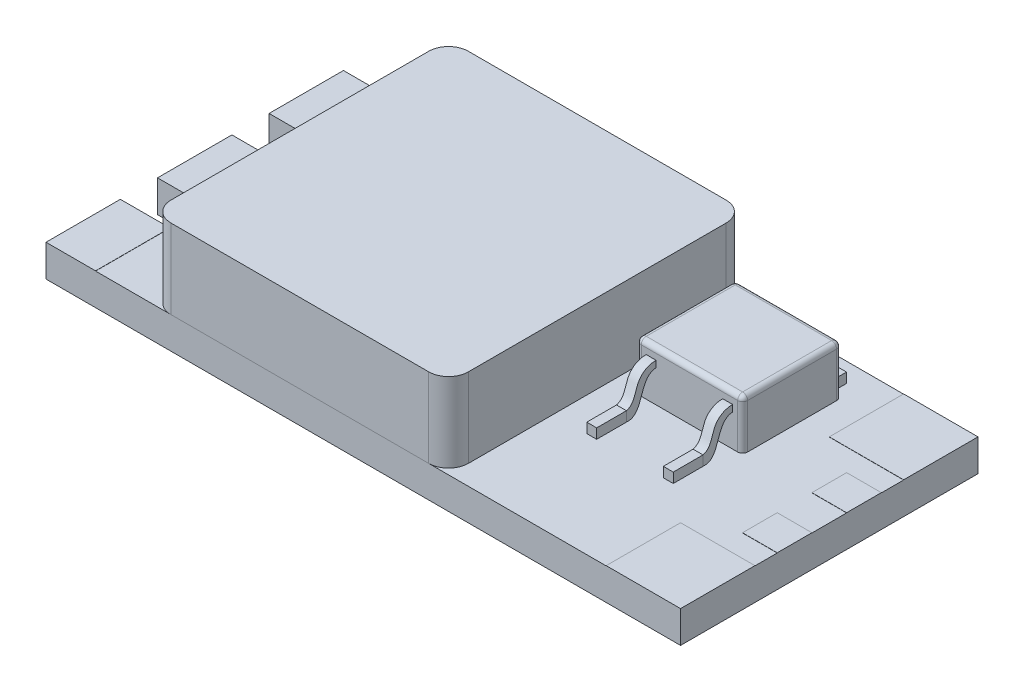
SolidWorks part; units mm, degrees
ref_plane "Front Plane" through (0, 0, 0) normal (0, 0, 1) x (1, 0, 0)
ref_plane "Top Plane" through (0, 0, 0) normal (0, 1, 0) x (1, 0, 0)
ref_plane "Right Plane" through (0, 0, 0) normal (1, 0, 0) x (0, 0, -1)
sketch "Sketch1" plane through (0, 0, 0) normal (0, 1, 0) x (1, 0, 0)
  line L0 (0, 3.75) -> (2.5, 3.75)
  line L1 (0, 0) -> (32, 0)
  line L2 (0, 0) -> (0, 3.75)
  line L3 (0, 15) -> (32, 15)
  line L4 (32, 0) -> (32, 15)
  line L5 (0, 0) -> (2.5, 0)
  line L6 (0, 0) -> (0, 3.75)
  line L7 (0, 15) -> (2.5, 15)
  line L8 (2.5, 3.75) -> (2.5, 5.625)
  line L9 (0, 11.25) -> (2.5, 11.25)
  line L10 (0, 11.25) -> (0, 15)
  line L11 (0, 9.375) -> (2.5, 9.375)
  line L12 (0, 9.375) -> (0, 5.625)
  line L13 (0, 5.625) -> (2.5, 5.625)
  line L15 (0, 11.25) -> (0, 15)
  line L16 (0, 5.625) -> (0, 9.375)
  line L17 (0, 5.625) -> (0, 9.375)
  line L18 (2.5, 9.375) -> (2.5, 11.25)
  dimension "D1" = 15
  dimension "D2" = 32
  dimension "D3" = 2.5
  dimension "D4" = 3.75
  dimension "D5" = 3.75
  dimension "D6" = 3.75
  dimension "D7" = 1.875
extrude "Boss-Extrude1" add sketch "Sketch1" along normal blind 1.6 contours L18 L11 L12 L13 L8 L0 L2 L1 L4 L3 L10 L9
sketch "Sketch2" plane through (0, 1.6, 0) normal (0, 1, 0) x (1, 0, 0)
  line L0 (0, 0) -> (32, 0) construction
  line L1 (5.3, 0) -> (20.3, 0)
  line L2 (5.3, 0) -> (5.3, 15)
  line L3 (5.3, 15) -> (20.3, 15)
  line L4 (20.3, 0) -> (20.3, 15)
  line L5 (0, 15) -> (32, 15) construction
  line L6 (0, 9.375) -> (0, 5.625) construction
  dimension "D1" = 5.3
  dimension "D2" = 15
extrude "Boss-Extrude2" add sketch "Sketch2" along normal blind 4 separate body
fillet "Fillet1" radius 1 4 edges at (20.3, 3.6, 0) (20.3, 3.6, -15) (5.3, 3.6, -15) (5.3, 3.6, 0)
sketch "Sketch3" plane through (0, 1.6, 0) normal (0, 1, 0) x (1, 0, 0)
  line L0 (32, 7.5) -> (33.6122, 7.5)
  line L1 (0, 15) -> (2.5, 15)
  line L2 (0, 15) -> (0, 3.75)
  line L3 (0, 3.75) -> (2.5, 3.75)
  line L4 (2.5, 15) -> (2.5, 3.75)
  line L5 (0, 0) -> (2.5, 0)
  line L6 (0, 0) -> (0, 3.75)
  line L7 (0, 3.75) -> (2.5, 3.75)
  line L8 (2.5, 0) -> (2.5, 3.75)
  line L9 (32, 0) -> (28.25, 0)
  line L10 (32, 0) -> (32, 3.75)
  line L11 (32, 3.75) -> (28.25, 3.75)
  line L12 (2.5, 11.25) -> (2.5, 9.375)
  line L13 (2.5, 9.375) -> (0, 9.375)
  line L14 (0, 9.375) -> (0, 5.625)
  line L15 (0, 5.625) -> (2.5, 5.625)
  line L16 (2.5, 5.625) -> (2.5, 3.75)
  line L17 (2.5, 3.75) -> (0, 3.75)
  line L18 (0, 3.75) -> (0, 0)
  line L19 (0, 0) -> (32, 0)
  line L20 (32, 0) -> (32, 15)
  line L21 (32, 15) -> (0, 15)
  line L22 (0, 15) -> (0, 11.25)
  line L23 (0, 11.25) -> (2.5, 11.25)
  line L24 (2.5, 11.25) -> (2.5, 9.375)
  line L25 (2.5, 9.375) -> (0, 9.375)
  line L26 (0, 9.375) -> (0, 5.625)
  line L27 (0, 5.625) -> (2.5, 5.625)
  line L28 (2.5, 5.625) -> (2.5, 3.75)
  line L29 (2.5, 3.75) -> (0, 3.75)
  line L30 (0, 3.75) -> (0, 0)
  line L31 (0, 0) -> (32, 0)
  line L32 (32, 0) -> (32, 15)
  line L33 (32, 15) -> (0, 15)
  line L34 (0, 15) -> (0, 11.25)
  line L35 (0, 11.25) -> (2.5, 11.25)
  line L36 (28.25, 0) -> (28.25, 3.75)
  line L37 (32, 6.625) -> (30.25, 6.625)
  line L38 (32, 6.625) -> (32, 4.875)
  line L39 (32, 4.875) -> (30.25, 4.875)
  line L40 (30.25, 6.625) -> (30.25, 4.875)
  line L41 (30.25, 8.375) -> (30.25, 10.125)
  line L42 (32, 10.125) -> (30.25, 10.125)
  line L43 (32, 8.375) -> (32, 10.125)
  line L44 (32, 8.375) -> (30.25, 8.375)
  line L45 (28.25, 15) -> (28.25, 11.25)
  line L46 (32, 11.25) -> (28.25, 11.25)
  line L47 (32, 15) -> (32, 11.25)
  line L48 (32, 15) -> (28.25, 15)
  line M27 (2.5, 9.375) -> (0, 9.375)
  line M28 (0, 9.375) -> (0, 5.625)
  line M29 (0, 5.625) -> (2.5, 5.625)
  line M31 (2.5, 3.75) -> (0, 3.75)
  line M32 (0, 3.75) -> (0, 0)
  line M33 (0, 0) -> (32, 0)
  line M34 (32, 0) -> (32, 15)
  line M35 (32, 15) -> (0, 15)
  line M36 (0, 15) -> (0, 11.25)
  line M37 (0, 11.25) -> (2.5, 11.25)
  dimension "D2" = 3.75
  dimension "D3" = 3.75
  dimension "D4" = 1.75
  dimension "D5" = 1.75
  dimension "D6" = 0.875
  dimension "D1" = 0
extrude "Boss-Extrude3" add sketch "Sketch3" along normal blind 0.01 contours L46 L45 M34 M35 | L44 L32 L42 L41 | L37 L40 L39 L32 | L36 L11 M33 M34 | L4 M35 M36 M37 | L4 M27 M28 M29 | L8 M33 M31 M32
sketch "Sketch4" plane through (0, 1.6, 0) normal (0, 1, 0) x (1, 0, 0)
  line L1 (21.4824, 13.2754) -> (26.844, 13.2754)
  line L2 (21.4824, 13.2754) -> (21.4824, 8.2878)
  line L3 (21.4824, 8.2878) -> (26.844, 8.2878)
  line L4 (26.844, 13.2754) -> (26.844, 8.2878)
extrude "Boss-Extrude4" add sketch "Sketch4" along normal blind 2.5 contours L2 L1 L4 L3
sketch "Sketch6" plane through (0, 1.6, 0) normal (0, 1, 0) x (1, 0, 0)
  line L1 (21.9824, 13.2754) -> (26.344, 13.2754)
  line L2 (21.9824, 13.2754) -> (21.9824, 14.0254)
  line L3 (21.9824, 14.0254) -> (26.344, 14.0254)
  line L4 (21.4824, 8.2878) -> (26.844, 8.2878)
  line L5 (26.844, 8.2878) -> (26.844, 13.2754)
  line L6 (26.844, 13.2754) -> (21.4824, 13.2754)
  line L7 (21.4824, 13.2754) -> (21.4824, 8.2878)
  line L8 (21.4824, 8.2878) -> (26.844, 8.2878)
  line L9 (26.844, 8.2878) -> (26.844, 13.2754)
  line L10 (26.844, 13.2754) -> (21.4824, 13.2754)
  line L11 (21.4824, 13.2754) -> (21.4824, 8.2878)
  line L12 (26.344, 13.2754) -> (26.344, 14.0254)
  line L14 (21.9824, 8.2878) -> (22.4824, 8.2878)
  line L15 (21.9824, 8.2878) -> (21.9824, 5.2878)
  line L16 (21.9824, 5.2878) -> (22.4824, 5.2878)
  line L17 (22.4824, 8.2878) -> (22.4824, 5.2878)
  line L18 (26.344, 8.2878) -> (25.844, 8.2878)
  line L19 (26.344, 8.2878) -> (26.344, 5.2878)
  line L20 (26.344, 5.2878) -> (25.844, 5.2878)
  line L21 (25.844, 8.2878) -> (25.844, 5.2878)
  line L22 (25.844, 5.2878) -> (26.344, 5.2878)
  line L23 (25.844, 5.2878) -> (25.844, 6.6282)
  line L25 (26.344, 5.2878) -> (26.344, 6.6282)
  line L26 (21.9824, 5.2878) -> (22.4824, 5.2878)
  line L27 (21.9824, 5.2878) -> (21.9824, 6.7878)
  line L28 (21.9824, 6.7878) -> (22.4824, 6.7878)
  line L29 (22.4824, 5.2878) -> (22.4824, 6.7878)
  line L30 (25.844, 5.2878) -> (26.344, 5.2878)
  line L31 (25.844, 5.2878) -> (25.844, 6.7878)
  line L32 (25.844, 6.7878) -> (26.344, 6.7878)
  line L33 (26.344, 5.2878) -> (26.344, 6.7878)
  line M38 (21.4824, 13.2754) -> (26.844, 13.2754)
  dimension "D2" = 0.75
  dimension "D3" = 0.5
  dimension "D4" = 0.5
  dimension "D5" = 0.5
  dimension "D6" = 0.5
  dimension "D7" = 0.5
  dimension "D8" = 0.5
  dimension "D9" = 3
  dimension "D10" = 3
  dimension "D1" = 0
extrude "Boss-Extrude5" add sketch "Sketch6" along normal blind 0.5 separate body contours L32 L21 L20 L19 | L28 L15 L16 L17 | L12 L3 L2 M38
sketch "Sketch7" plane through (26.344, 0, 0) normal (1, 0, 0) x (0, 0, -1)
  line L0 (8.2878, 4.1) -> (8.2878, 1.6) construction
  line L1 (8.2878, 3.2266) -> (8.2878, 3.5498)
  line L5 (5.2878, 1.6) -> (6.7878, 1.6)
  line L6 (6.7878, 1.6) -> (6.7878, 2.1)
  line L7 (6.7878, 2.1) -> (5.2878, 2.1)
  line L8 (5.2878, 2.1) -> (5.2878, 1.6)
  line L9 (5.2878, 1.6) -> (6.7878, 1.6)
  line L10 (6.7878, 1.6) -> (6.7878, 2.1)
  line L11 (6.7878, 2.1) -> (5.2878, 2.1)
  line L12 (5.2878, 2.1) -> (5.2878, 1.6)
  spline S0 degree 3 poles (6.7878, 1.6) (7.7188, 1.5101) (7.3747, 3.1846) (8.2878, 3.2266) knots 0 0 0 0 1 1 1 1
  spline S1 degree 3 poles (6.7878, 2.1) (7.2302, 2.2154) (7.1923, 3.1943) (7.9475, 3.5661) (8.2878, 3.5498) knots 0 0 0 0 0.555689 1 1 1 1
  line M6 (6.7878, 1.6) -> (6.7878, 2.1)
  dimension "D1" = 0
extrude "Boss-Extrude6" add sketch "Sketch7" against normal blind 0.5 separate body contours S1 S0 L1 M6
sketch "Sketch8" plane through (22.4824, 0, 0) normal (1, 0, 0) x (0, 0, -1)
  line L2 (6.7878, 2.1) -> (6.7878, 1.6)
  line L3 (8.2878, 3.2266) -> (8.2878, 3.5498)
  line L4 (6.7878, 2.1) -> (6.7878, 1.6)
  line L5 (8.2878, 3.2266) -> (8.2878, 3.5498)
  spline S2 degree 3 poles (-3511.9072, -1889.7291) (155.4518, -85.1759) (-86.9811, 79.1505) (67.1071, -60.0327) (-3013.5054, 2624.1531) knots -12.718445 -12.718445 -12.718445 -12.718445 0.444311 9.641193 9.641193 9.641193 9.641193 only from (8.2878, 3.5498) to (6.7878, 2.1)
  spline S3 degree 3 poles (-2392.4799, 3201.947) (2401.1783, -3225.8398) (-2391.0138, 3226.8555) (2422.4372, -3185.8128) knots -9.307914 -9.307914 -9.307914 -9.307914 10.335231 10.335231 10.335231 10.335231 only from (6.7878, 1.6) to (8.2878, 3.2266)
  spline S4 degree 3 poles (8.2878, 3.5498) (7.9475, 3.5661) (7.1923, 3.1943) (7.2302, 2.2154) (6.7878, 2.1) knots 0 0 0 0 0.444311 1 1 1 1
  spline S5 degree 3 poles (6.7878, 1.6) (7.7188, 1.5101) (7.3747, 3.1846) (8.2878, 3.2266) knots 0 0 0 0 1 1 1 1
  dimension "D1" = 0
extrude "Boss-Extrude7" add sketch "Sketch8" against normal blind 0.5 separate body
fillet "Fillet2" radius 0.25 4 edges at (21.4824, 2.85, -13.2754) (21.4824, 2.85, -8.2878) (26.844, 2.85, -8.2878) (26.844, 2.85, -13.2754)
fillet "Fillet3" radius 0.25 8 edges at (26.7708, 4.1, -13.2021) (26.844, 4.1, -10.7816) (26.7708, 4.1, -8.361) (24.1632, 4.1, -8.2878) (21.5557, 4.1, -8.361) (21.4824, 4.1, -10.7816) (21.5557, 4.1, -13.2021) (24.1632, 4.1, -13.2754)
